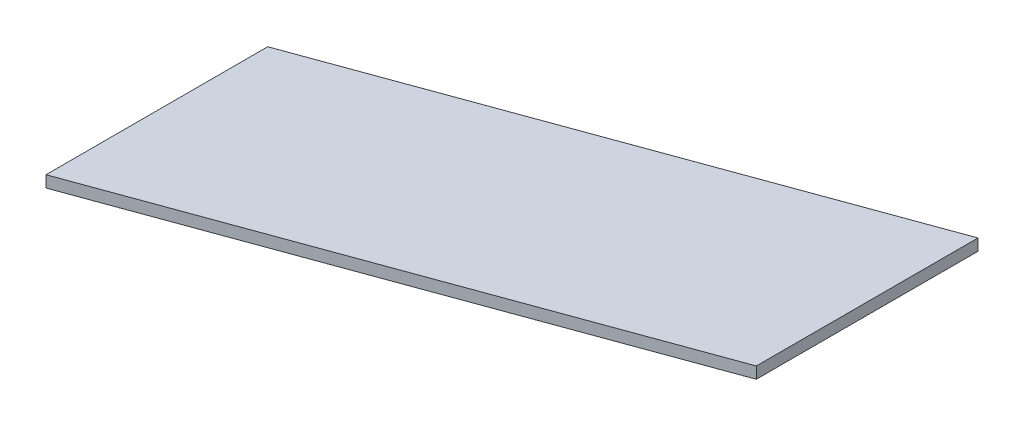
SolidWorks part; units mm, degrees
material "Balsa"
ref_plane "Front Plane" through (0, 0, 0) normal (0, 0, 1) x (1, 0, 0)
ref_plane "Top Plane" through (0, 0, 0) normal (0, 1, 0) x (1, 0, 0)
ref_plane "Right Plane" through (0, 0, 0) normal (1, 0, 0) x (0, 0, -1)
sketch "Sketch1" plane through (0, 0, 0) normal (0, 1, 0) x (1, 0, 0)
  line L0 (0, -60.96) -> (0, 0)
  line L1 (0, 0) -> (143.2092, 52.1239)
  line L2 (143.2092, 52.1239) -> (143.2092, -8.8361)
  line L3 (143.2092, -8.8361) -> (0, -60.96)
  dimension "D1" = 152.4
  dimension "D2" = 60.96
  dimension "D3" = 110
extrude "Boss-Extrude1" add sketch "Sketch1" along normal blind 3.175
